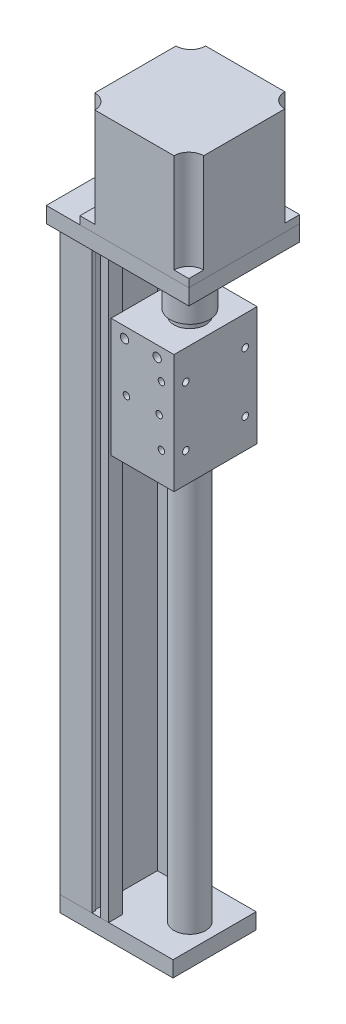
SolidWorks part; units mm, degrees
ref_plane "Front Plane" through (0, 0, 0) normal (0, 0, 1) x (1, 0, 0)
ref_plane "Top Plane" through (0, 0, 0) normal (0, 1, 0) x (1, 0, 0)
ref_plane "Right Plane" through (0, 0, 0) normal (1, 0, 0) x (0, 0, -1)
sketch "Sketch1" plane through (0, 0, 0) normal (0, 1, 0) x (1, 0, 0)
  line L1 (0, 21) -> (57, 21)
  line L2 (0, 21) -> (0, -21)
  line L3 (0, -21) -> (57, -21)
  line L4 (57, 21) -> (57, -21)
  point P4 (0, 0)
  dimension "D1" = 57
  dimension "D2" = 42
extrude "Boss-Extrude1" add sketch "Sketch1" along normal blind 8
sketch "Sketch2" plane through (0, 8, 0) normal (0, 1, 0) x (1, 0, 0)
  line L0 (0, 21) -> (0, -21)
  line L1 (0, -21) -> (24.5, -21)
  line L2 (0, -21) -> (57, -21) construction
  line L3 (24.5, -21) -> (24.5, -14)
  line L4 (24.5, -14) -> (14.1, -14)
  line L5 (14.1, -14) -> (14.1, 14)
  line L6 (14.1, 14) -> (24.5, 14)
  line L7 (24.5, 14) -> (24.5, 21)
  line L8 (57, 21) -> (0, 21) construction
  line L9 (24.5, 21) -> (0, 21)
  dimension "D1" = 24.5
  dimension "D2" = 7
  dimension "D3" = 10.4
extrude "Boss-Extrude2" add sketch "Sketch2" along normal blind 297
sketch "Sketch3" plane through (0, 305, 0) normal (0, 1, 0) x (1, 0, 0)
  line L1 (0, 28) -> (72, 28)
  line L2 (0, 28) -> (0, -28)
  line L3 (0, -28) -> (72, -28)
  line L4 (72, 28) -> (72, -28)
  point P4 (0, 0)
  dimension "D1" = 56
  dimension "D2" = 72
extrude "Boss-Extrude3" add sketch "Sketch3" along normal blind 8
sketch "Sketch4" plane through (0, 313, 0) normal (0, 1, 0) x (1, 0, 0)
  line L0 (0, -28) -> (72, -28) construction
  line L1 (72, 28) -> (17, 28)
  line L2 (72, 28) -> (72, -28)
  line L3 (72, -28) -> (17, -28)
  line L4 (17, 28) -> (17, -28)
  line L5 (57, -21) -> (57, 21) construction
  line L6 (57, -21) -> (57, 21) construction
  point P7 (44.5, 28)
  dimension "D1" = 55
extrude "Boss-Extrude4" add sketch "Sketch4" along normal blind 54
sketch "Sketch5" plane through (0, 367, 0) normal (0, 1, 0) x (1, 0, 0)
  line L0 (17, 28) -> (17, 20.5)
  line L1 (17, 28) -> (17, -28) construction
  line L2 (17, 28) -> (24.5, 28)
  line L3 (44.5, 28) -> (44.5, 12.3616) construction
  line L4 (72, 28) -> (17, 28) construction
  line L5 (72, 28) -> (64.5, 28)
  line L6 (72, 28) -> (72, 20.5)
  line L7 (17, 0) -> (32.1173, 0) construction
  line L8 (72, -28) -> (72, -20.5)
  line L9 (72, -28) -> (64.5, -28)
  line L10 (17, -28) -> (24.5, -28)
  line L11 (17, -28) -> (17, -20.5)
  arc A0 (24.5, 28) -> (17, 20.5) centre (17, 28) cw
  arc A1 (64.5, 28) -> (72, 20.5) centre (72, 28) ccw
  arc A2 (64.5, -28) -> (72, -20.5) centre (72, -28) cw
  arc A3 (24.5, -28) -> (17, -20.5) centre (17, -28) ccw
  dimension "D1" = 7.5
extrude "Cut-Extrude1" cut sketch "Sketch5" against normal blind 50
sketch "Sketch6" plane through (0, 8, 0) normal (0, 1, 0) x (1, 0, 0)
  line L0 (57, -21) -> (57, 21) construction
  circle A0 centre (44.5, 0) radius 8
  point P5 (0, 0)
  dimension "D1" = 16
  dimension "D2" = 12.5
extrude "Boss-Extrude5" add sketch "Sketch6" along normal blind 268.3
ref_plane "Plane1" through (0, 243, 0) normal (0, 1, 0) x (1, 0, 0)
sketch "Sketch7" plane through (0, 243, 0) normal (0, 1, 0) x (1, 0, 0)
  line L0 (24.5, -21) -> (24.5, -14) construction
  line L1 (25.7, -21) -> (57.5, -21)
  line L2 (25.7, -21) -> (25.7, 21)
  line L3 (25.7, 21) -> (57.5, 21)
  line L4 (57.5, -21) -> (57.5, 21)
  line L5 (24.5, -21) -> (57, -21) construction
  line L6 (57, 21) -> (24.5, 21) construction
  line L7 (0, 21) -> (0, -21) construction
  dimension "D1" = 1.2
  dimension "D2" = 57.5
extrude "Boss-Extrude6" add sketch "Sketch7" along normal mid plane 60
sketch "Sketch8" plane through (0, 276.3, 0) normal (0, 1, 0) x (1, 0, 0)
  circle A0 centre (44.5, 0) radius 10
  dimension "D1" = 20
extrude "Boss-Extrude7" add sketch "Sketch8" along normal blind 25
sketch "Sketch9" plane through (0, 305, 0) normal (0, -1, 0) x (1, 0, 0)
  circle A0 centre (44.5, 0) radius 15
  circle A1 centre (44.5, 0) radius 10
  circle A2 centre (44.5, 0) radius 10 construction
  dimension "D2" = 30
  dimension "D1" = 0
extrude "Cut-Extrude2" cut sketch "Sketch9" against normal blind 5
sketch "Sketch10" plane through (0, 301.3, 0) normal (0, 1, 0) x (1, 0, 0)
  circle A0 centre (44.5, 0) radius 3.175
  dimension "D1" = 6.35
extrude "Boss-Extrude8" add sketch "Sketch10" along normal up to next
sketch "Sketch11" plane through (0, 0, -21) normal (0, 0, -1) x (-1, 0, 0)
  line L0 (-24.5, 305) -> (0, 305) construction
  line L1 (-20.3, 305) -> (-16, 305)
  line L2 (-20.3, 305) -> (-20.3, 8)
  line L3 (-20.3, 8) -> (-16, 8)
  line L4 (-16, 305) -> (-16, 8)
  line L5 (-57, 8) -> (-24.5, 8) construction
  line L6 (0, 305) -> (0, 0) construction
  dimension "D1" = 16
  dimension "D2" = 4.3
extrude "Cut-Extrude3" cut sketch "Sketch11" against normal blind 5.4
ref_plane "Plane2" through (18.15, 0, 0) normal (1, 0, 0) x (0, 0, -1)
sketch "Sketch12" plane through (18.15, 0, 0) normal (1, 0, 0) x (0, 0, -1)
  line L0 (15.6, 305) -> (15.6, 8) construction
  line L1 (19.2, 8) -> (15.6, 8)
  line L2 (19.2, 8) -> (19.2, 305)
  line L3 (19.2, 305) -> (15.6, 305)
  line L4 (15.6, 8) -> (15.6, 305)
  line L5 (28, 305) -> (21, 305) construction
  line L6 (15.6, 8) -> (21, 8) construction
  line L7 (21, 305) -> (21, 8) construction
  dimension "D1" = 1.8
extrude "Cut-Extrude4" cut sketch "Sketch12" against normal mid plane 5.4
mirror "Mirror1" about plane through (0, 0, 0) normal (0, 0, 1) of "Cut-Extrude3", "Cut-Extrude4"
sketch "Sketch13" plane through (0, 0, 0) normal (-1, 0, 0) x (0, 0, 1)
  line L0 (21, 8) -> (-21, 8) construction
  line L1 (21, 8) -> (-21, 8) construction
  line L3 (17.15, 305) -> (12.85, 305)
  line L4 (17.15, 305) -> (17.15, 8)
  line L5 (17.15, 8) -> (12.85, 8)
  line L6 (12.85, 305) -> (12.85, 8)
  line L7 (21, 305) -> (28, 305) construction
  line L8 (0, 313) -> (0, 348.5706) construction
  line L9 (-28, 313) -> (28, 313) construction
  point P17 (15, 305)
  dimension "D1" = 15
  dimension "D2" = 4.3
extrude "Cut-Extrude5" cut sketch "Sketch13" against normal blind 6.8
ref_plane "Plane3" through (0, 0, 15) normal (0, 0, 1) x (1, 0, 0)
sketch "Sketch14" plane through (0, 0, 15) normal (0, 0, 1) x (1, 0, 0)
  line L0 (6.8, 305) -> (0, 305) construction
  line L1 (2, 8) -> (5.3, 8)
  line L2 (2, 8) -> (2, 305)
  line L3 (2, 305) -> (5.3, 305)
  line L4 (5.3, 8) -> (5.3, 305)
  line L5 (6.8, 8) -> (0, 8) construction
  line L6 (6.8, 305) -> (6.8, 8) construction
  line L7 (0, 305) -> (0, 8) construction
  dimension "D1" = 1.5
  dimension "D2" = 2
extrude "Cut-Extrude6" cut sketch "Sketch14" against normal mid plane 6.8
mirror "Mirror2" about plane through (0, 0, 0) normal (0, 0, 1) of "Cut-Extrude6", "Cut-Extrude5"
sketch "Sketch15" plane through (57.5, 0, 0) normal (1, 0, 0) x (0, 0, -1)
  line L0 (-21, 273) -> (21, 273) construction
  line L1 (-15, 228) -> (15, 228)
  line L2 (-15, 228) -> (-15, 258)
  line L3 (-15, 258) -> (15, 258)
  line L4 (15, 228) -> (15, 258)
  line L5 (-15, 228) -> (15, 258) construction
  line L6 (-15, 258) -> (15, 228) construction
  line L7 (-21, 273) -> (-21, 213) construction
  point P0 (0, 243)
  point P5 (0, 273)
  point P6 (-21, 243)
  dimension "D1" = 30
  dimension "D2" = 30
hole_wizard "M4x0.7 Tapped Hole1" positions "Sketch19" profile "Sketch18" tap size "M4x0.7" standard "ANSI Metric"
sketch "Sketch19" plane through (57.5, 0, 0) normal (1, 0, 0) x (0, 0, -1)
  point P0 (-15, 258)
  point P3 (15, 258)
  point P6 (15, 228)
  point P9 (-15, 228)
sketch "Sketch18" plane through (57.5, 258, 15) normal (0, 1, 0) x (0, 0, -1)
  line L0 (0, 0) -> (0, 11.0914)
  line L1 (0, 11.0914) -> (1.65, 10.1)
  line L2 (1.65, 10.1) -> (1.65, 0)
  line L5 (1.65, 0) -> (0, 0)
  line L10 (0, 11.0914) -> (-1.65, 10.1) construction
  line L11 (0, -6.35) -> (0, 107.95) construction
  dimension "Tap Drill Dia." = 3.3
  dimension "Tap Drill Depth" = 10.1
  dimension "Drill Angle" = 118
cosmetic thread "Hole Thread1" parameters "D1"=8, "D2"=4
cosmetic thread "Hole Thread2" parameters "D1"=8, "D2"=4
cosmetic thread "Hole Thread3" parameters "D1"=8, "D2"=4
cosmetic thread "Hole Thread4" parameters "D1"=8, "D2"=4
ref_plane "Plane5" through (0, 8, 0) normal (0, 1, 0) x (1, 0, 0)
ref_plane "Plane6" through (0, 313, 0) normal (0, 1, 0) x (1, 0, 0)
ref_plane "Plane7" through (0, 305, 0) normal (0, -1, 0) x (-1, 0, 0)
split line "Split Line4"
split line "Split Line5"
split line "Split Line6"
sketch "Sketch20" plane through (0, 0, 0) normal (0, 0, 1) x (1, 0, 0)
  line L0 (36.5, 276.3) -> (52.5, 276.3) construction
  line L1 (27, 268) -> (62, 268) construction
  line L2 (27, 268) -> (27, 208) construction
  line L3 (27, 208) -> (62, 208) construction
  line L4 (62, 268) -> (62, 208) construction
  line L5 (24.5, 8) -> (57, 8) construction
  line L6 (27, 68) -> (62, 68) construction
  line L7 (27, 68) -> (27, 8) construction
  line L8 (27, 8) -> (62, 8) construction
  line L9 (62, 68) -> (62, 8) construction
  line L10 (44.5, 268) -> (44.5, 68) construction
  line L11 (44.5, 168) -> (94.5, 168)
  line L12 (44.5, 178) -> (94.5, 178) construction
  line L13 (44.5, 158) -> (94.5, 158) construction
  point P4 (44.5, 276.3)
  point P5 (62, 238)
  point P12 (44.5, 68)
  point P19 (62, 38)
  dimension "D1" = 60
  dimension "D2" = 60
  dimension "D3" = 200
  dimension "D4" = 35
  dimension "D5" = 10
  dimension "D6" = 50
  dimension "D7" = 10
sketch "Sketch21" plane through (0, 0, 0) normal (0, 0, 1) x (1, 0, 0)
  line L0 (44.5, 213) -> (44.5, 13.0745) construction
  line L1 (59.5, 73) -> (29.5, 73)
  line L2 (59.5, 73) -> (59.5, 13)
  line L3 (59.5, 13) -> (29.5, 13)
  line L4 (29.5, 73) -> (29.5, 13)
  line L5 (36.5, 213) -> (52.5, 213) construction
  line L7 (59.5, 243) -> (59.5, 43) construction
  line L8 (29.5, 273) -> (59.5, 273)
  line L9 (29.5, 273) -> (29.5, 213)
  line L10 (29.5, 213) -> (59.5, 213)
  line L11 (59.5, 273) -> (59.5, 213)
  line L12 (59.5, 143) -> (259.5525, 143) construction
  line L13 (57, 8) -> (24.5, 8) construction
  point P8 (44.5, 73)
  point P11 (59.5, 43)
  point P16 (44.5, 273)
  point P17 (59.5, 243)
  dimension "D1" = 60
  dimension "D2" = 30
  dimension "D3" = 5
  dimension "D4" = 200
sketch "Sketch22" plane through (0, 0, 21) normal (0, 0, 1) x (1, 0, 0)
  line L0 (57.5, 243) -> (25.7, 243) construction
  line L1 (57.5, 273) -> (57.5, 213) construction
  line L2 (25.7, 273) -> (25.7, 213) construction
  line L3 (57.5, 258) -> (25.7, 258) construction
  line L4 (25.7, 273) -> (57.5, 273) construction
  point P8 (51.15, 258)
  point P9 (50, 243)
  point P10 (33.5, 243)
  point P11 (51.15, 228)
  point P12 (49, 267.5)
  point P13 (32.5, 267.5)
  dimension "D1" = 30
  dimension "D2" = 6.35
  dimension "D3" = 7.5
  dimension "D4" = 16.5
  dimension "D5" = 8.5
  dimension "D6" = 16.5
  dimension "D7" = 5.5
hole_wizard "M4x0.7 Tapped Hole2" positions "Sketch22" profile "Sketch23" tap size "M4x0.7" standard "ANSI Metric"
sketch "Sketch23" plane through (51.15, 228, 21) normal (1, 0, 0) x (0, -1, 0)
  line L0 (0, 0) -> (0, 6.9914)
  line L1 (0, 6.9914) -> (1.65, 6)
  line L2 (1.65, 6) -> (1.65, 0)
  line L5 (1.65, 0) -> (0, 0)
  line L10 (0, 6.9914) -> (-1.65, 6) construction
  line L11 (0, -6.35) -> (0, 107.95) construction
  dimension "Tap Drill Dia." = 3.3
  dimension "Tap Drill Depth" = 6
  dimension "Drill Angle" = 118
cosmetic thread "Hole Thread5" parameters "D1"=8, "D2"=4
cosmetic thread "Hole Thread6" parameters "D1"=8, "D2"=4
cosmetic thread "Hole Thread7" parameters "D1"=8, "D2"=4
cosmetic thread "Hole Thread8" parameters "D1"=8, "D2"=4
sketch "Sketch24" plane through (0, 0, 21) normal (0, 0, 1) x (1, 0, 0)
  line L0 (49, 267.5) -> (32.5, 267.5) construction
  line L1 (57.5, 273) -> (57.5, 213) construction
  line L2 (25.7, 273) -> (57.5, 273) construction
  point P0 (49, 267.5)
  point P1 (32.5, 267.5)
  point P10 (49, 267.5)
  point P13 (32.5, 267.5)
  dimension "D1" = 8.5
  dimension "D2" = 16.5
  dimension "D3" = 5.5
hole_wizard "M5x0.8 Tapped Hole1" positions "Sketch24" profile "Sketch25" tap size "M5x0.8" standard "ANSI Metric"
sketch "Sketch25" plane through (32.5, 267.5, 21) normal (1, 0, 0) x (0, -1, 0)
  line L0 (0, 0) -> (0, 11.2618)
  line L1 (0, 11.2618) -> (2.1, 10)
  line L2 (2.1, 10) -> (2.1, 0)
  line L5 (2.1, 0) -> (0, 0)
  line L10 (0, 11.2618) -> (-2.1, 10) construction
  line L11 (0, -6.35) -> (0, 107.95) construction
  dimension "Tap Drill Dia." = 4.2
  dimension "Tap Drill Depth" = 10
  dimension "Drill Angle" = 118
cosmetic thread "Hole Thread9" parameters "D1"=10, "D2"=5
cosmetic thread "Hole Thread10" parameters "D1"=10, "D2"=5
mirror "Mirror3" about plane through (0, 0, 0) normal (0, 0, 1) of "M5x0.8 Tapped Hole1", "M4x0.7 Tapped Hole2"
cosmetic thread "Hole Thread11" parameters "D1"=10, "D2"=5
cosmetic thread "Hole Thread12" parameters "D1"=8, "D2"=4
cosmetic thread "Hole Thread13" parameters "D1"=8, "D2"=4
cosmetic thread "Hole Thread14" parameters "D1"=10, "D2"=5
cosmetic thread "Hole Thread15" parameters "D1"=8, "D2"=4
cosmetic thread "Hole Thread16" parameters "D1"=8, "D2"=4
ref_plane "Plane8" through (0, 143, 0) normal (0, -1, 0) x (-1, 0, 0)
ref_plane "Plane9" through (0, 168, 0) normal (0, -1, 0) x (-1, 0, 0)
equation "\"D2@Sketch15\"=\"D1@Sketch15\""
equation "\"D7@Sketch20\"=\"D5@Sketch20\""
